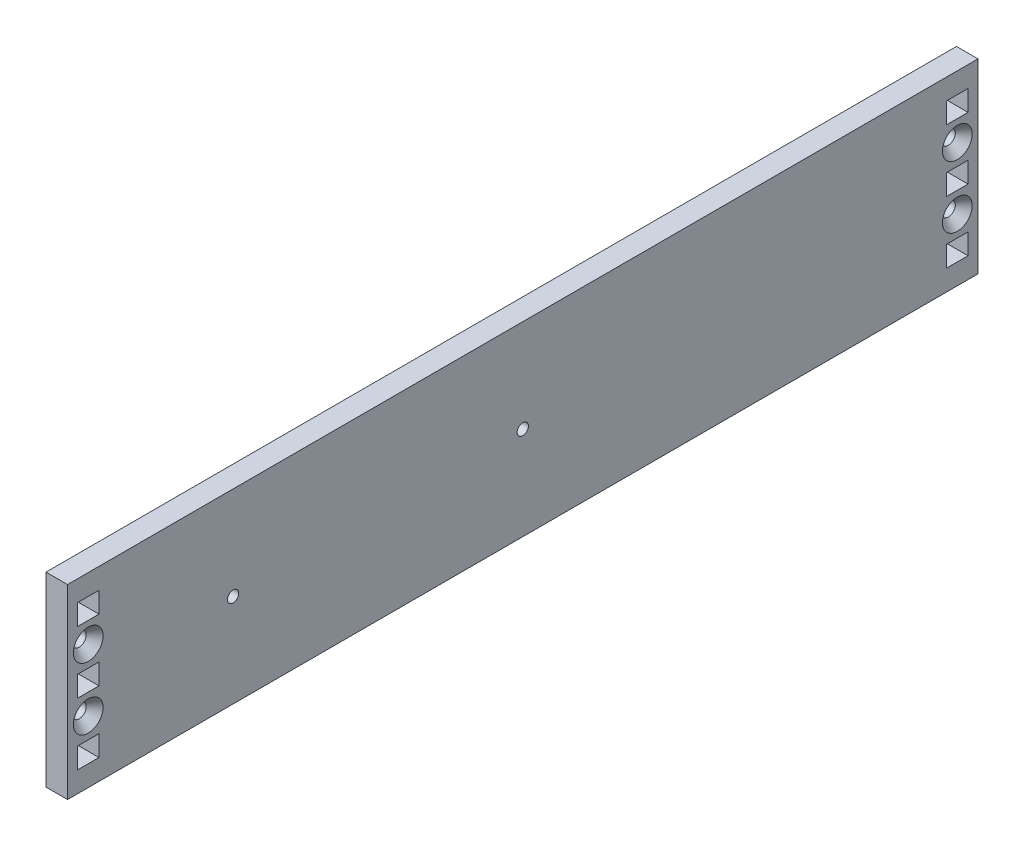
SolidWorks part; units mm, degrees
material "Acrylic (BLUE)"
ref_plane "Front Plane" through (0, 0, 0) normal (0, 0, 1) x (1, 0, 0)
ref_plane "Top Plane" through (0, 0, 0) normal (0, 1, 0) x (1, 0, 0)
ref_plane "Right Plane" through (0, 0, 0) normal (1, 0, 0) x (0, 0, -1)
sketch "Sketch1" plane through (0, 0, 0) normal (1, 0, 0) x (0, 0, -1)
  line L0 (0, 0) -> (0, 28.575) construction
  line L1 (-139.7, 28.575) -> (139.7, 28.575)
  line L2 (-139.7, 28.575) -> (-139.7, -28.575)
  line L3 (-139.7, -28.575) -> (139.7, -28.575)
  line L4 (139.7, 28.575) -> (139.7, -28.575)
  line L5 (-130.048, 0) -> (0, 0) construction
  line L6 (0, 0) -> (130.048, 0) construction
  line L7 (0, 0) -> (0, -28.575) construction
  line B0 (-130.048, 3.175) -> (-130.048, -3.175)
  line B1 (-130.048, -3.175) -> (-136.652, -3.175)
  line B2 (-136.652, -3.175) -> (-136.652, 3.175)
  line B3 (-136.652, 3.175) -> (-130.048, 3.175)
  line B4 (-130.048, 22.225) -> (-130.048, 15.875)
  line B5 (-130.048, 15.875) -> (-136.652, 15.875)
  line B6 (-136.652, 15.875) -> (-136.652, 22.225)
  line B7 (-136.652, 22.225) -> (-130.048, 22.225)
  circle B8 centre (-133.35, 9.525) radius 2.1526
  line B9 (-130.048, -15.875) -> (-130.048, -22.225)
  line B10 (-130.048, -22.225) -> (-136.652, -22.225)
  line B11 (-136.652, -15.875) -> (-136.652, -22.225)
  line B12 (-130.048, -15.875) -> (-136.652, -15.875)
  circle B13 centre (-133.35, -9.525) radius 2.1527
  line B14 (136.652, 3.175) -> (136.652, -3.175)
  line B15 (136.652, -3.175) -> (130.048, -3.175)
  line B16 (130.048, -3.175) -> (130.048, 3.175)
  line B17 (130.048, 3.175) -> (136.652, 3.175)
  line B18 (136.652, 22.225) -> (136.652, 15.875)
  line B19 (136.652, 15.875) -> (130.048, 15.875)
  line B20 (130.048, 15.875) -> (130.048, 22.225)
  line B21 (130.048, 22.225) -> (136.652, 22.225)
  circle B22 centre (133.35, 9.525) radius 2.1526
  line B23 (136.652, -15.875) -> (136.652, -22.225)
  line B24 (136.652, -22.225) -> (130.048, -22.225)
  line B25 (130.048, -15.875) -> (130.048, -22.225)
  line B26 (136.652, -15.875) -> (130.048, -15.875)
  circle B27 centre (133.35, -9.525) radius 2.1527
  dimension "D1" = 266.7
  dimension "D2" = 57.15
  dimension "D3" = 6.35
  dimension "D4" = 6.35
sketch_block_instance "BOLT_HOLE_2X-1"
sketch_block "BOLT_HOLE_2X" parameters "D1"=4.3053, "D2"=6.35, "D3"=6.35, "D4"=6.604
sketch_block_instance "BOLT_HOLE_2X-2"
extrude "Boss-Extrude1" add sketch "Sketch1" along normal blind 6.604
hole_wizard "CSK for #8 Flat Head Socket Cap Screw1" positions "Sketch3" profile "Sketch2" countersink size "#8" standard "ANSI Inch" end condition through all
sketch "Sketch3" plane through (6.604, 0, 0) normal (1, 0, 0) x (0, 0, -1)
  point P0 (-133.35, 9.525)
  point P3 (-133.35, -9.525)
  point P6 (133.35, 9.525)
  point P9 (133.35, -9.525)
sketch "Sketch2" plane through (6.604, 9.525, 133.35) normal (0, 1, 0) x (0, 0, -1)
  line L0 (0, 0) -> (0, 6.604)
  line L1 (0, 6.604) -> (2.1526, 6.604)
  line L2 (2.1526, 6.604) -> (2.1526, 2.7685)
  line L3 (2.1526, 2.7685) -> (4.5593, 0)
  line L5 (4.5593, 0) -> (0, 0)
  line L6 (-2.1526, 2.7685) -> (-4.5593, 0) construction
  line L11 (0, -6.35) -> (0, 107.95) construction
  dimension "Thru Hole Dia." = 4.3053
  dimension "Thru Hole Depth" = 6.604
  dimension "Near C'Sink Dia." = 9.1186
  dimension "Near C'Sink Angle" = 82
hole_wizard "#8-32 Tapped Hole1" positions "Sketch5" profile "Sketch4" tap size "#8-32" standard "ANSI Inch"
sketch "Sketch5" plane through (6.604, 0, 0) normal (1, 0, 0) x (0, 0, -1)
  line L0 (-139.7, 0) -> (-88.9, 0) construction
  line L1 (-139.7, 28.575) -> (-139.7, -28.575) construction
  line L2 (-88.9, 0) -> (0, 0) construction
  point P2 (-88.9, 0)
  point P7 (0, 0)
  dimension "D1" = 139.7
  dimension "D2" = 50.8
sketch "Sketch4" plane through (6.604, 0, 88.9) normal (0, 1, 0) x (0, 0, -1)
  line L0 (0, 0) -> (0, 11.7566)
  line L1 (0, 11.7566) -> (1.7272, 10.7188)
  line L2 (1.7272, 10.7188) -> (1.7272, 0)
  line L5 (1.7272, 0) -> (0, 0)
  line L10 (0, 11.7566) -> (-1.7272, 10.7188) construction
  line L11 (0, -6.35) -> (0, 107.95) construction
  dimension "Tap Drill Dia." = 3.4544
  dimension "Tap Drill Depth" = 10.7188
  dimension "Drill Angle" = 118
other "Move Face1" [suppressed] parameters "D1"=0.0508
